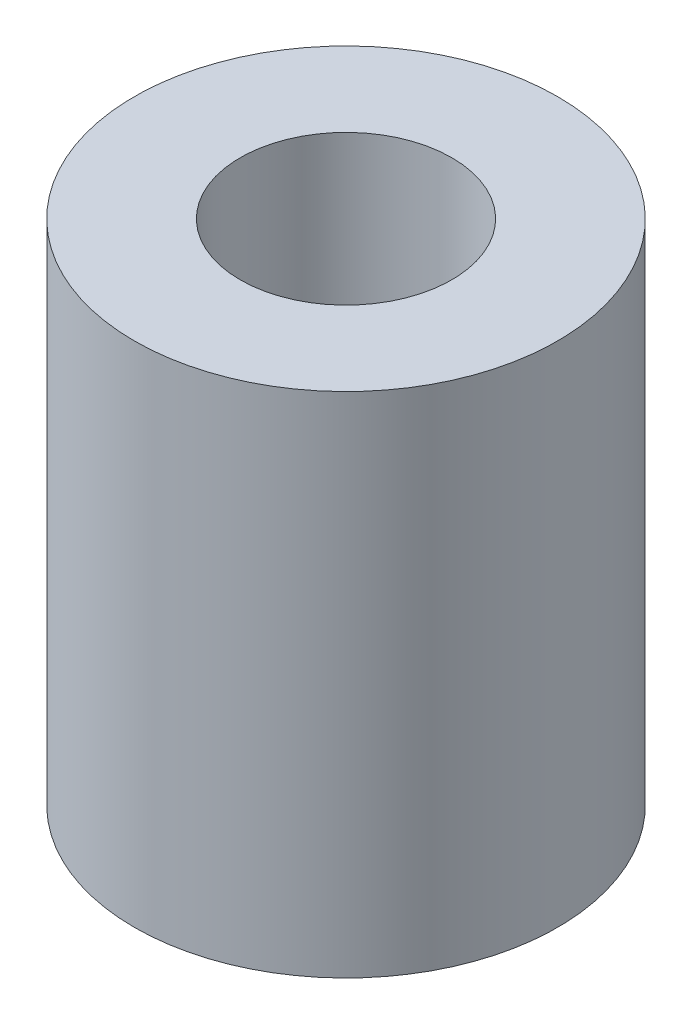
SolidWorks part; units mm, degrees
ref_plane "前视基准面" through (0, 0, 0) normal (0, 0, 1) x (1, 0, 0)
ref_plane "上视基准面" through (0, 0, 0) normal (0, 1, 0) x (1, 0, 0)
ref_plane "右视基准面" through (0, 0, 0) normal (1, 0, 0) x (0, 0, -1)
sketch "草图1" plane through (0, 0, 0) normal (0, 1, 0) x (1, 0, 0)
  circle A0 centre (0, 0) radius 10
  dimension "D1" = 20
extrude "凸台-拉伸1" add sketch "草图1" along normal blind 24
sketch "草图3" plane through (0, 24, 0) normal (0, 1, 0) x (1, 0, 0)
  circle A0 centre (0, 0) radius 5
  dimension "D1" = 10
extrude "切除-拉伸1" cut sketch "草图3" against normal blind 12
sketch "草图4" plane through (0, 0, 0) normal (0, -1, 0) x (1, 0, 0)
  circle A0 centre (0, 0) radius 2.5
  dimension "D1" = 5
extrude "切除-拉伸2" cut sketch "草图4" against normal blind 12
